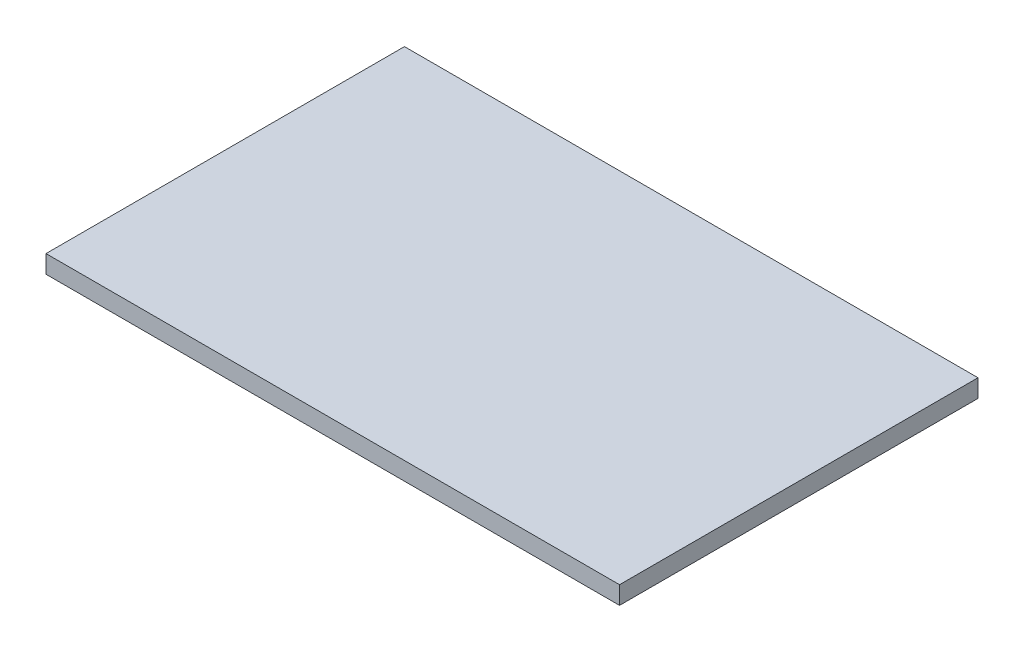
SolidWorks part; units mm, degrees
material "Ceramic Porcelain"
ref_plane "Front Plane" through (0, 0, 0) normal (0, 0, 1) x (1, 0, 0)
ref_plane "Top Plane" through (0, 0, 0) normal (0, 1, 0) x (1, 0, 0)
ref_plane "Right Plane" through (0, 0, 0) normal (1, 0, 0) x (0, 0, -1)
sketch "Sketch1" plane through (0, 0, 0) normal (0, 1, 0) x (1, 0, 0)
  line L1 (-45.8454, -22.0075) -> (114.1546, -22.0075)
  line L2 (-45.8454, -22.0075) -> (-45.8454, 77.9925)
  line L3 (-45.8454, 77.9925) -> (114.1546, 77.9925)
  line L4 (114.1546, -22.0075) -> (114.1546, 77.9925)
  dimension "D1" = 160
  dimension "D2" = 100
extrude "Boss-Extrude1" add sketch "Sketch1" along normal blind 5
